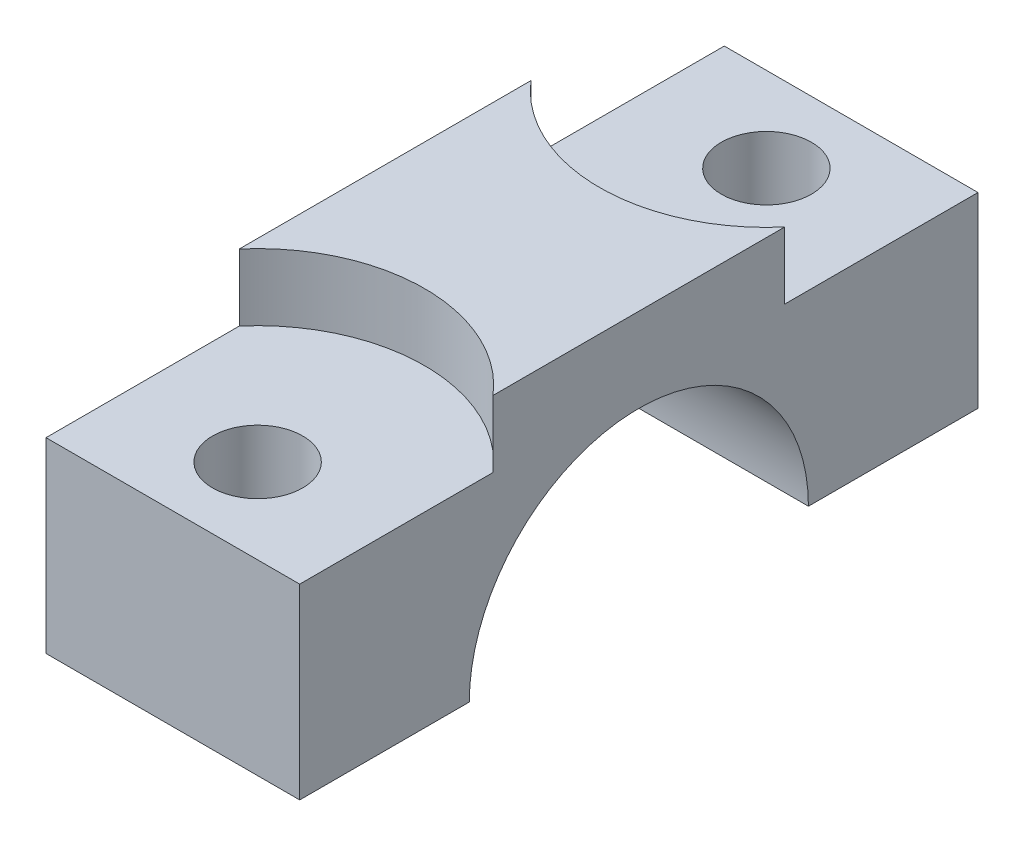
SolidWorks part; units mm, degrees
ref_plane "Front Plane" through (0, 0, 0) normal (0, 0, 1) x (1, 0, 0)
ref_plane "Top Plane" through (0, 0, 0) normal (0, 1, 0) x (1, 0, 0)
ref_plane "Right Plane" through (0, 0, 0) normal (1, 0, 0) x (0, 0, -1)
sketch "Sketch2" plane through (0, 0, 0) normal (1, 0, 0) x (0, 0, -1)
  line L0 (12.7, 0) -> (25.4, 0)
  line L1 (-25.4, 0) -> (-12.7, 0)
  line L2 (-25.4, 0) -> (-25.4, 19)
  line L3 (-25.4, 19) -> (25.4, 19)
  line L4 (25.4, 0) -> (25.4, 19)
  arc A0 (-12.7, 0) -> (12.7, 0) centre (0, 0) cw
  point P8 (0, 19)
  point P9 (0, 0)
  point P10 (0, 0)
  dimension "D3" = 12.7
  dimension "D1" = 50.8
  dimension "D2" = 19
extrude "Boss-Extrude1" add sketch "Sketch2" along normal mid plane 19
sketch "Sketch3" plane through (0, 0, 0) normal (0, -1, 0) x (1, 0, 0)
  line L0 (-9.5, 19.05) -> (9.5, 19.05) construction
  line L1 (-9.5, 25.4) -> (-9.5, 12.7) construction
  line L2 (9.5, 25.4) -> (9.5, 12.7) construction
  line L3 (-9.5, -19.05) -> (9.5, -19.05) construction
  line L4 (-9.5, -12.7) -> (-9.5, -25.4) construction
  line L5 (9.5, -12.7) -> (9.5, -25.4) construction
  point P12 (0, 19.05)
  point P13 (0, -19.05)
hole_wizard "CBORE for M12 Hex Head Cap Screw1" positions "Sketch6" profile "Sketch5" counterbore size "M12" standard "ISO" end condition through all
sketch "Sketch6" plane through (0, 19, 0) normal (0, 1, 0) x (1, 0, 0)
  point P0 (0, 19.05)
  point P3 (0, -19.05)
sketch "Sketch5" plane through (0, 19, -19.05) normal (1, 0, 0) x (0, 0, 1)
  line L0 (0, 0) -> (0, 19)
  line L1 (0, 19) -> (3.375, 19)
  line L3 (3.375, 19) -> (3.375, 5)
  line L4 (3.375, 5) -> (12.5, 5)
  line L5 (12.5, 5) -> (12.5, 0)
  line L7 (12.5, 0) -> (0, 0)
  line L11 (0, -6.35) -> (0, 107.95) construction
  dimension "Thru Hole Dia." = 6.75
  dimension "Thru Hole Depth" = 19
  dimension "C'Bore Dia." = 25
  dimension "C'Bore Depth" = 5
